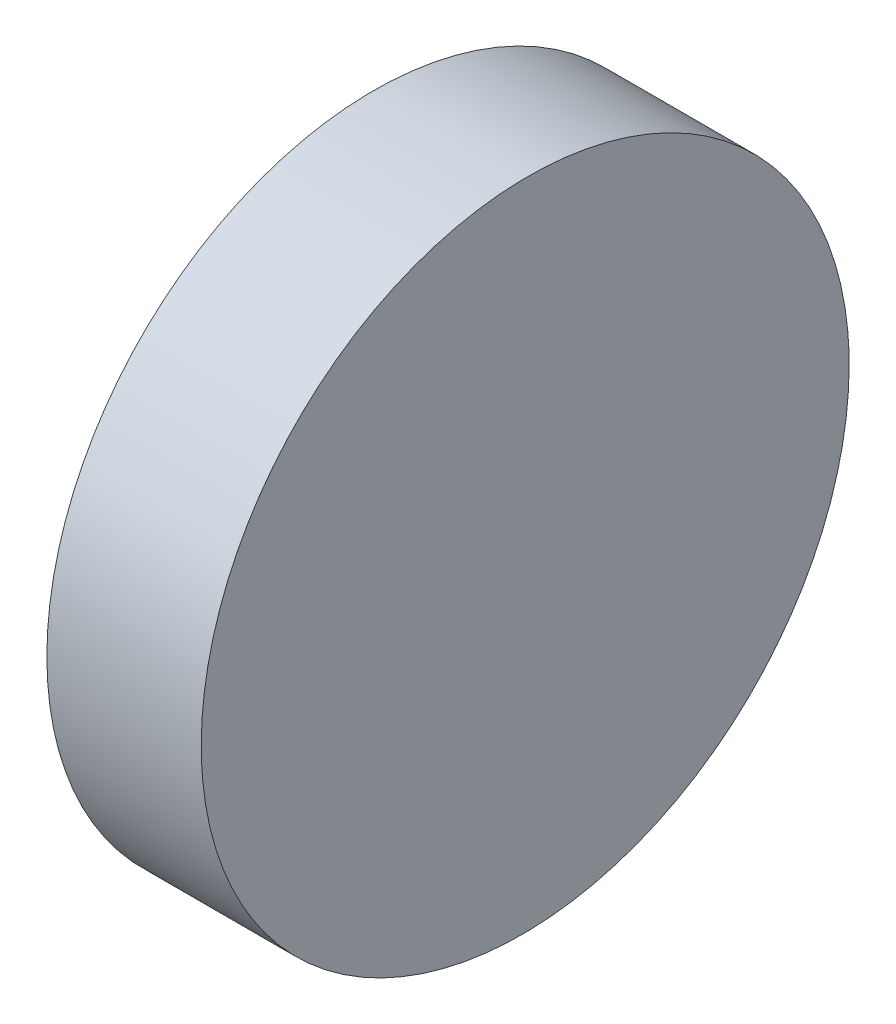
SolidWorks part; units mm, degrees
ref_plane "前视基准面" through (0, 0, 0) normal (0, 0, 1) x (1, 0, 0)
ref_plane "上视基准面" through (0, 0, 0) normal (0, 1, 0) x (1, 0, 0)
ref_plane "右视基准面" through (0, 0, 0) normal (1, 0, 0) x (0, 0, -1)
sketch "草图1" plane through (0, 0, 0) normal (0, 1, 0) x (1, 0, 0)
  line L0 (-12.1202, 0) -> (19.0875, 0) construction
  line L1 (0, 6.35) -> (0, -6.35)
  line L2 (0, -6.35) -> (3, -6.35)
  line L3 (3, -6.35) -> (2.8892, 6.35)
  line L4 (0, 6.35) -> (2.8892, 6.35)
  point P5 (0, 0)
  dimension "D1" = 3
  dimension "D2" = 12.7
  dimension "D3" = 0.5
extrude "凸台-拉伸1" add sketch "草图1" along normal blind 12.7
sketch "草图5" plane through (0, 0, 0) normal (-1, 0, 0) x (0, 0, 1)
  line L0 (0, 0) -> (0, 12.7) construction
  line L1 (-6.35, 12.7) -> (6.35, 12.7) construction
  line L2 (0, 12.7) -> (0.9302, 12.292) construction
  line L3 (-6.35, 6.35) -> (6.35, 6.35) construction
  line L4 (-6.35, 12.7) -> (-6.35, 0) construction
  line L5 (6.35, 12.7) -> (6.35, 0) construction
  line L6 (6.35, 6.35) -> (6.6453, 6.1075) construction
  line L11 (-6.35, 0) -> (6.35, 0)
  line L12 (6.35, 0) -> (6.35, 12.7)
  line L13 (6.35, 12.7) -> (-6.35, 12.7)
  line L14 (-6.35, 12.7) -> (-6.35, 0)
  line L15 (-6.35, 0) -> (6.35, 0)
  line L16 (6.35, 0) -> (6.35, 12.7)
  line L17 (6.35, 12.7) -> (-6.35, 12.7)
  line L18 (-6.35, 12.7) -> (-6.35, 0)
  circle A0 centre (0, 6.35) radius 6.35
  line M5 (-6.35, 0) -> (6.35, 0)
  line M6 (6.35, 0) -> (6.35, 12.7)
  line M7 (6.35, 12.7) -> (-6.35, 12.7)
  line M8 (-6.35, 12.7) -> (-6.35, 0)
  dimension "D1" = 12.7
  dimension "D2" = 0
extrude "切除-拉伸2" cut sketch "草图5" against normal blind 12.5 contours A0 L17 M8 | A0 L18 M5 | A0 L15 M6 | A0 L16 M7
